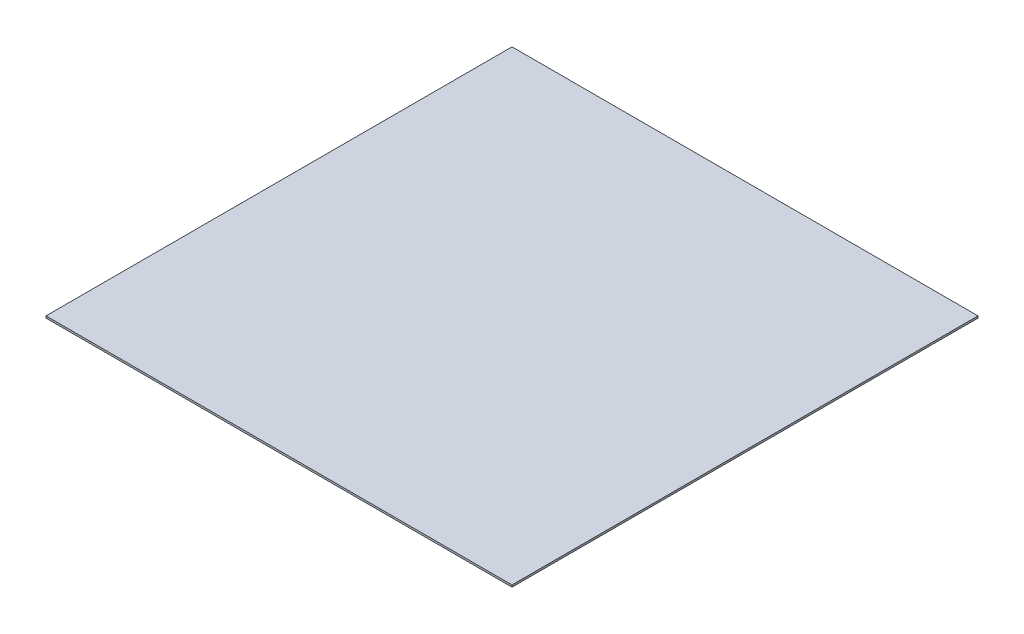
SolidWorks part; units mm, degrees
ref_plane "Front Plane" through (0, 0, 0) normal (0, 0, 1) x (1, 0, 0)
ref_plane "Top Plane" through (0, 0, 0) normal (0, 1, 0) x (1, 0, 0)
ref_plane "Right Plane" through (0, 0, 0) normal (1, 0, 0) x (0, 0, -1)
sketch "Sketch1" plane through (0, 0, 0) normal (0, 1, 0) x (1, 0, 0)
  line L1 (-762, -762) -> (762, -762)
  line L2 (-762, -762) -> (-762, 762)
  line L3 (-762, 762) -> (762, 762)
  line L4 (762, -762) -> (762, 762)
  line L5 (-762, -762) -> (762, 762) construction
  line L6 (-762, 762) -> (762, -762) construction
  point P0 (0, 0)
  dimension "D1" = 1524
  dimension "D2" = 1524
extrude "Boss-Extrude1" add sketch "Sketch1" along normal mid plane 6.35
